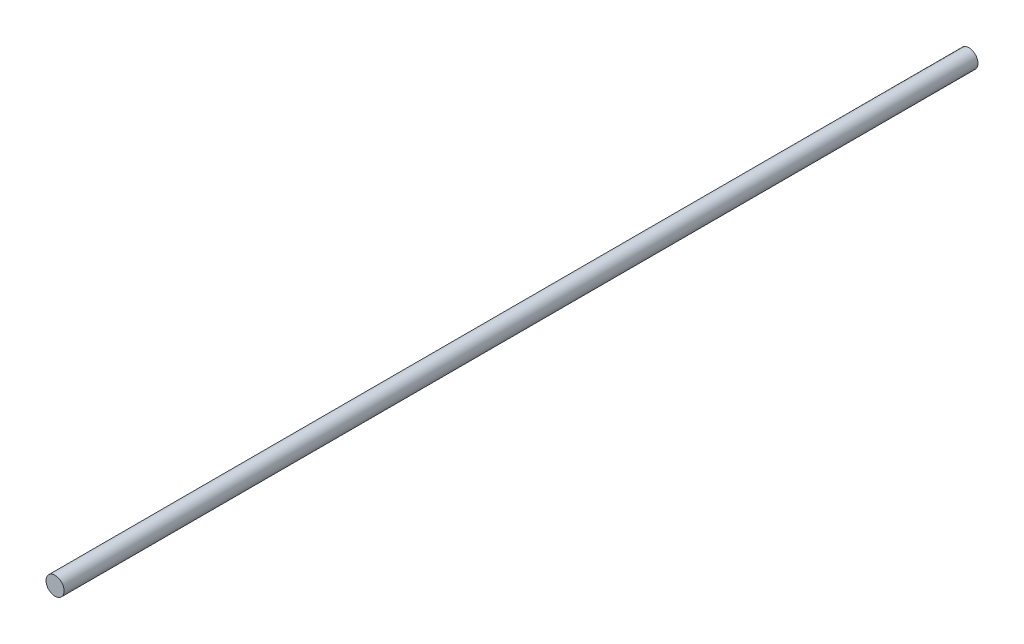
SolidWorks part; units mm, degrees
material "6061 Alloy"
ref_plane "Front Plane" through (0, 0, 0) normal (0, 0, 1) x (1, 0, 0)
ref_plane "Top Plane" through (0, 0, 0) normal (0, 1, 0) x (1, 0, 0)
ref_plane "Right Plane" through (0, 0, 0) normal (1, 0, 0) x (0, 0, -1)
sketch "Sketch1" plane through (0, 0, 0) normal (0, 0, 1) x (1, 0, 0)
  circle A0 centre (0, 0) radius 4
  dimension "D1" = 8
extrude "Boss-Extrude1" add sketch "Sketch1" along normal blind 330 and the other way blind 73
